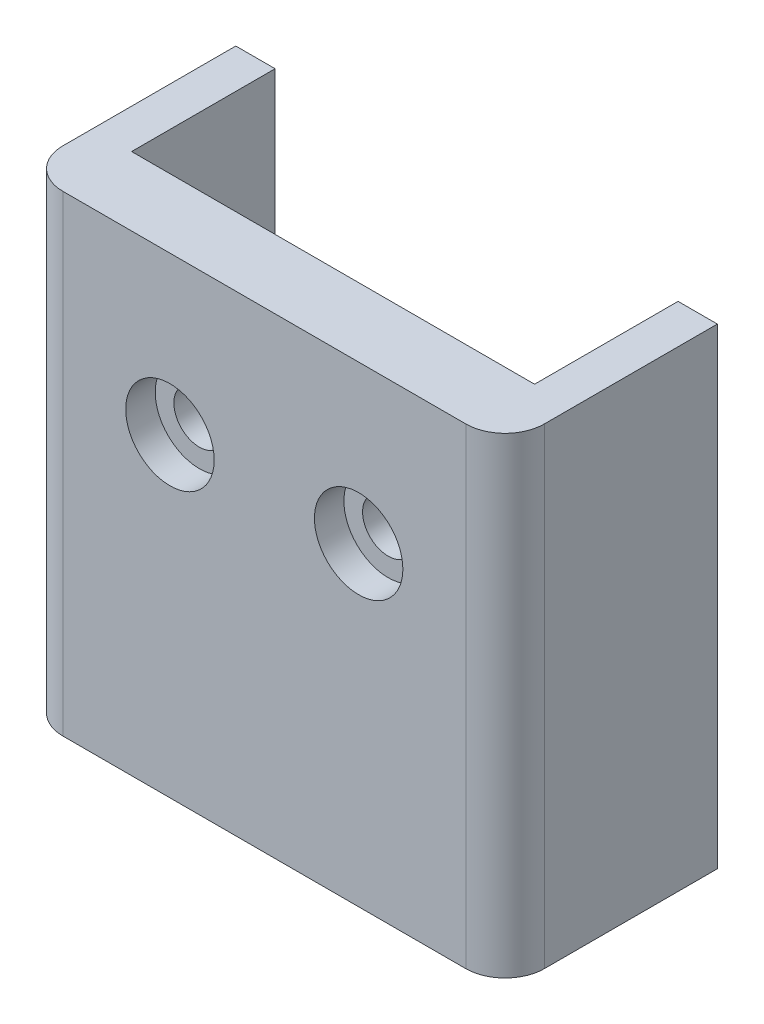
SolidWorks part; units mm, degrees
ref_plane "Front Plane" through (0, 0, 0) normal (0, 0, 1) x (1, 0, 0)
ref_plane "Top Plane" through (0, 0, 0) normal (0, 1, 0) x (1, 0, 0)
ref_plane "Right Plane" through (0, 0, 0) normal (1, 0, 0) x (0, 0, -1)
sketch "Sketch1" plane through (0, 0, 0) normal (0, 0, 1) x (1, 0, 0)
  line L0 (-10.25, 13) -> (10.25, 13)
  line L1 (-10.25, 13) -> (-10.25, -11)
  line L2 (-10.25, -11) -> (10.25, -11)
  line L3 (10.25, 13) -> (10.25, -11)
  line L4 (-4.8, 5) -> (4.8, 5) construction
  line L5 (0, -4) -> (0, -11) construction
  line L6 (0, 13) -> (0, 5) construction
  line L7 (0, 5) -> (0, 0) construction
  line L8 (0, 0) -> (0, -4) construction
  circle A1 centre (-4.8, 5) radius 1.3
  circle A2 centre (4.8, 5) radius 1.3
  circle A3 centre (0, -4) radius 3 construction
  point P14 (0, 5)
  dimension "D3" = 2.6
  dimension "D4" = 6
  dimension "D1" = 24
  dimension "D2" = 20.5
  dimension "D5" = 7
  dimension "D6" = 8
  dimension "D7" = 9.6
  dimension "D8" = 4
extrude "Boss-Extrude1" add sketch "Sketch1" along normal blind 3.5
sketch "Sketch2" plane through (0, -11, 0) normal (0, -1, 0) x (-1, 0, 0)
  line L1 (10.25, -3.5) -> (12.25, -3.5)
  line L2 (10.25, -3.5) -> (10.25, 15)
  line L3 (10.25, 15) -> (12.25, 15)
  line L4 (12.25, -3.5) -> (12.25, 15)
  line L5 (-10.25, -3.5) -> (-12.25, -3.5)
  line L6 (-10.25, -3.5) -> (-10.25, 15)
  line L7 (-10.25, 15) -> (-12.25, 15)
  line L8 (-12.25, -3.5) -> (-12.25, 15)
  dimension "D1" = 2
  dimension "D2" = 18.5
extrude "Boss-Extrude2" add sketch "Sketch2" against normal up to vertex (24 mm away)
sketch "Sketch3" plane through (0, -11, 0) normal (0, -1, 0) x (1, 0, 0)
  line L0 (0, 3.5) -> (0, 0) construction
  line L5 (-12.25, 3.5) -> (12.25, 3.5) construction
  line L6 (0, 0) -> (0, -15.097) construction
  line L11 (-3.75, -10.5) -> (3.75, -10.5) construction
  line L12 (-10.25, 0) -> (-3.75, 0)
  line L13 (-10.25, 0) -> (-10.25, -10.5)
  line L14 (-10.25, -10.5) -> (-3.75, -10.5)
  line L15 (-3.75, 0) -> (-3.75, -10.5)
  line L16 (10.25, 0) -> (3.75, 0)
  line L17 (10.25, 0) -> (10.25, -10.5)
  line L18 (10.25, -10.5) -> (3.75, -10.5)
  line L19 (3.75, 0) -> (3.75, -10.5)
  point P15 (0, -10.5)
  dimension "D1" = 10.5
  dimension "D3" = 7.5
extrude "Boss-Extrude3" add sketch "Sketch3" against normal blind 2
fillet "Fillet1" radius 3.5 2 edges at (3.75, -10, 0) (-3.75, -10, 0)
fillet "Fillet2" radius 2 2 edges at (-12.25, 1, 3.5) (12.25, 1, 3.5)
sketch "Sketch4" plane through (0, 0, 3.5) normal (0, 0, 1) x (1, 0, 0)
  circle A0 centre (-4.8, 5) radius 2.25
  circle A1 centre (4.8, 5) radius 2.25
  dimension "D1" = 4.5
extrude "Cut-Extrude1" cut sketch "Sketch4" against normal blind 1.5
fillet "Fillet4" radius 3 3 edges at (11.25, -11, -15) (11.25, 13, -15) (-11.25, 13, -15)
sketch "Sketch7" [suppressed] plane through (12.25, 0, 0) normal (1, 0, 0) x (0, 0, -1)
  line L0 (-1.0366, -11) -> (-1.0366, -2.5) construction
  line L1 (12, -11) -> (-1.5, -11) construction
  line L2 (0.7746, -2.5) -> (-1.0366, -2.5) construction
  line L4 (4.2746, -2.5) -> (16.1029, -2.5) construction
  line L5 (4.2746, 1) -> (16.1029, 1)
  line L6 (4.2746, -6) -> (16.1029, -6)
  arc A0 (4.2746, 1) -> (4.2746, -6) centre (4.2746, -2.5) ccw
  arc A1 (16.1029, -6) -> (16.1029, 1) centre (16.1029, -2.5) ccw
  point P9 (10.1887, -2.5)
  dimension "D1" = 3.5
  dimension "D2" = 8.5
extrude "Cut-Extrude4" [suppressed] cut sketch "Sketch7" against normal up to vertex
fillet "Fillet5" [suppressed] radius 1.5
sketch "Sketch9" plane through (0, 0, 0) normal (0, 0, -1) x (-1, 0, 0)
  line L1 (-10.25, -9) -> (-6.25, -9)
  line L2 (-10.25, -9) -> (-10.25, -6)
  line L3 (-10.25, -6) -> (-6.25, -6)
  line L4 (-6.25, -9) -> (-6.25, -6)
  line L5 (10.25, -9) -> (6.25, -9)
  line L6 (10.25, -9) -> (10.25, -6)
  line L7 (10.25, -6) -> (6.25, -6)
  line L8 (6.25, -9) -> (6.25, -6)
  dimension "D1" = 4
  dimension "D2" = 3
extrude "Boss-Extrude4" [suppressed] add sketch "Sketch9" along normal blind 6.5
sketch "Sketch10" [suppressed] plane through (12.25, 0, 0) normal (1, 0, 0) x (0, 0, -1)
  line L0 (15, -6) -> (4.2746, -6)
  line L1 (15, -6) -> (15, 1)
  line L2 (15, 1) -> (4.2746, 1)
  line L3 (15, 1) -> (4.2746, 1) construction
  arc A0 (4.2746, 1) -> (4.2746, -6) centre (4.2746, -2.5) ccw construction
  arc A1 (4.2746, 1) -> (4.2746, -6) centre (4.2746, -2.5) ccw
extrude "Boss-Extrude5" [suppressed] add sketch "Sketch10" against normal up to vertex
fillet "Fillet6" [suppressed] radius 1.5
sketch "Sketch13" plane through (0, 13, 0) normal (0, 1, 0) x (1, 0, 0)
  line L0 (0, -3.5) -> (0, 7.3) construction
  line L1 (10.25, -3.5) -> (-10.25, -3.5) construction
  line L2 (0, 7.3) -> (12.25, 7.3) construction
  line L3 (12.25, 12) -> (12.25, -1.5) construction
  line L5 (12.25, 7.3) -> (-12.25, 7.3)
  line L6 (12.25, 7.3) -> (12.25, 15)
  line L7 (12.25, 15) -> (-12.25, 15)
  line L8 (-12.25, 7.3) -> (-12.25, 15)
  dimension "D1" = 10.8
extrude "Cut-Extrude6" cut sketch "Sketch13" against normal through all
sketch "Sketch14" plane through (0, -11, 0) normal (0, -1, 0) x (1, 0, 0)
  line L0 (0, 0) -> (0, -3.3411) construction
  line L1 (-0.25, 0) -> (0.25, 0)
  line L2 (0, -3.3411) -> (0, -3.5) construction
  line L3 (-3.7464, -3.3411) -> (-1.9483, -3.3411)
  line L4 (-1.9483, -3.3411) -> (1.9483, -3.3411) construction
  line L5 (1.9483, -3.3411) -> (3.7464, -3.3411)
  arc A1 (-0.25, 0) -> (-3.7464, -3.3411) centre (-0.25, -3.5) ccw
  arc A2 (0.25, 0) -> (3.7464, -3.3411) centre (0.25, -3.5) cw
  circle A3 centre (0, -3.5) radius 1.9548 construction
  arc A4 (-1.9483, -3.3411) -> (1.9483, -3.3411) centre (0, -3.5) cw
extrude "Boss-Extrude6" add sketch "Sketch14" against normal up to vertex
sketch "Sketch15" plane through (0, -11, 0) normal (0, -1, 0) x (-1, 0, 0)
  line L0 (0, 1.5452) -> (0, 3.5) construction
  line L1 (1.9483, 3.3411) -> (3.7464, 3.3411)
  line L2 (-1.9483, 3.3411) -> (-3.7464, 3.3411)
  circle A1 centre (0, 3.5) radius 3.7466 construction
  arc A2 (-1.9483, 3.3411) -> (1.9483, 3.3411) centre (0, 3.5) ccw construction
  circle A3 centre (0, 3.5) radius 1.9548 construction
  arc A4 (3.7464, 3.3411) -> (-3.7464, 3.3411) centre (0, 3.5033) cw
  arc A5 (1.9483, 3.3411) -> (-1.9483, 3.3411) centre (0, 3.5) cw
  dimension "D2" = 3.9095
extrude "Boss-Extrude7" add sketch "Sketch15" along normal blind 2
